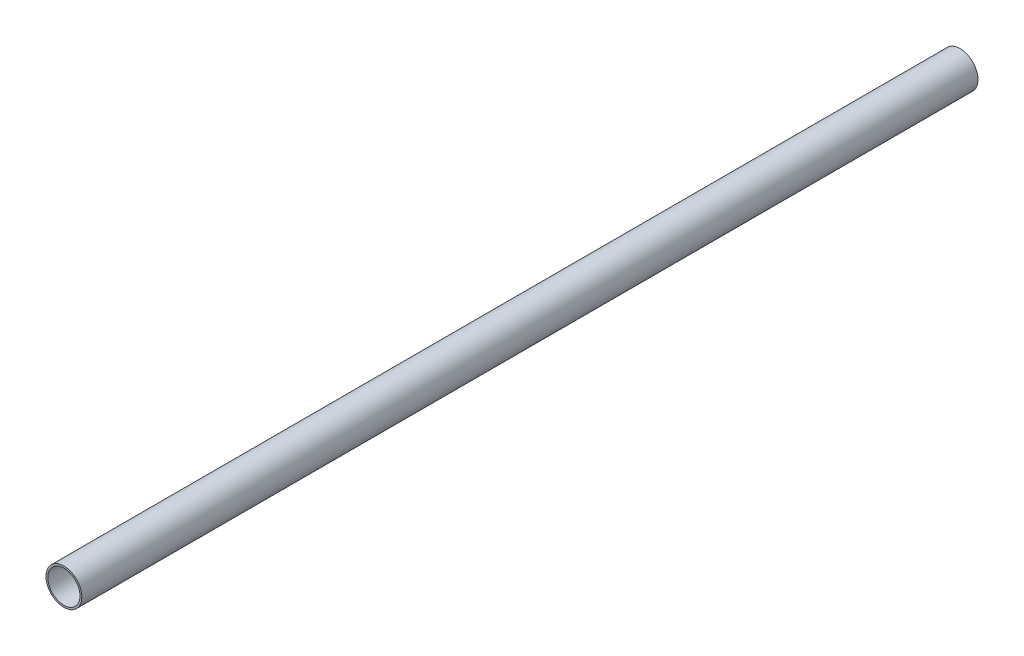
SolidWorks part; units mm, degrees
ref_plane "Front Plane" through (0, 0, 0) normal (0, 0, 1) x (1, 0, 0)
ref_plane "Top Plane" through (0, 0, 0) normal (0, 1, 0) x (1, 0, 0)
ref_plane "Right Plane" through (0, 0, 0) normal (1, 0, 0) x (0, 0, -1)
sketch "Sketch1" plane through (0, 0, 0) normal (0, 0, 1) x (1, 0, 0)
  circle A0 centre (0, 0) radius 20
  circle A1 centre (0, 0) radius 18
  dimension "D1" = 40
  dimension "D2" = 2
extrude "Boss-Extrude1" add sketch "Sketch1" along normal blind 1000
